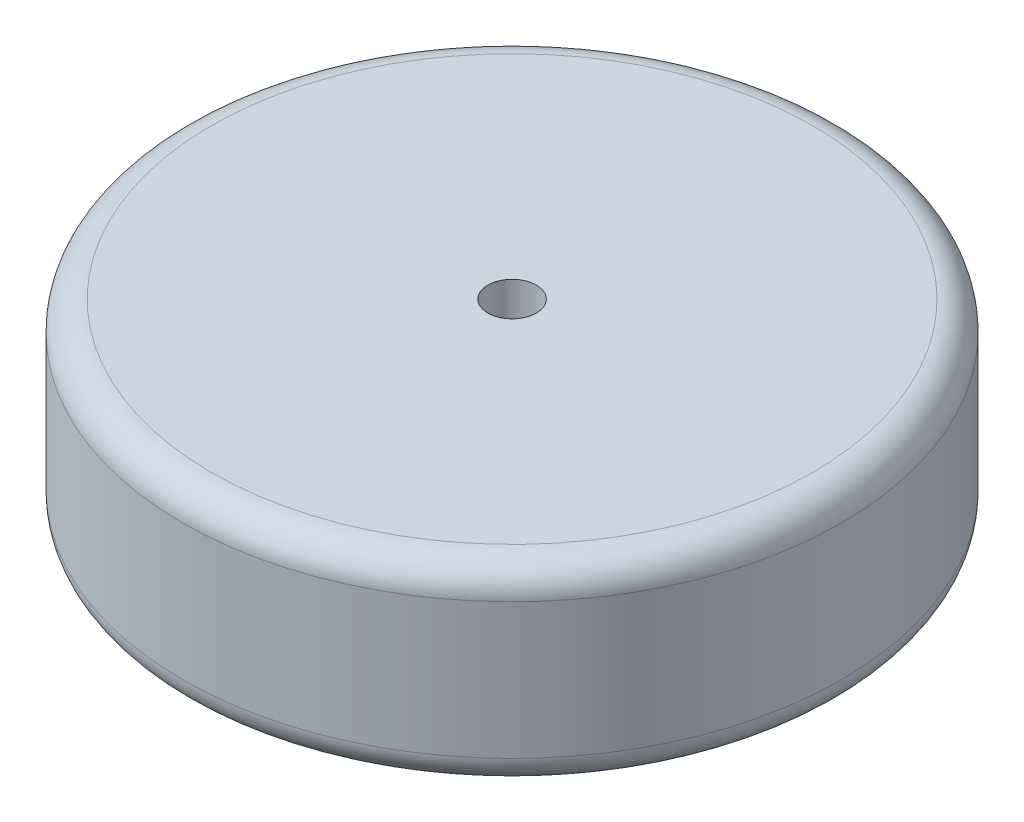
SolidWorks part; units mm, degrees
ref_plane "前基準面" through (0, 0, 0) normal (0, 0, 1) x (1, 0, 0)
ref_plane "上基準面" through (0, 0, 0) normal (0, 1, 0) x (1, 0, 0)
ref_plane "右基準面" through (0, 0, 0) normal (1, 0, 0) x (0, 0, -1)
sketch "草圖1" plane through (0, 0, 0) normal (0, 1, 0) x (1, 0, 0)
  circle A0 centre (0, 0) radius 34
  circle A1 centre (0, 0) radius 2.5
  dimension "D1" = 68
  dimension "D2" = 5
extrude "填料-伸長1" add sketch "草圖1" along normal blind 20
fillet "圓角1" radius 3 2 edges at (0, 0, 34) (0, 20, 34)
